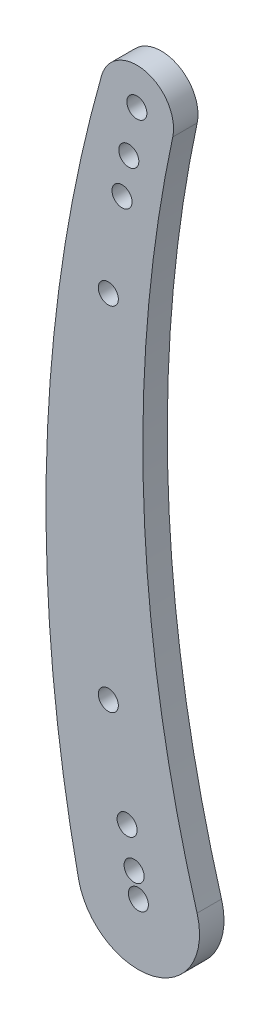
SolidWorks part; units mm, degrees
material "Acrílico (Impacto medio-alto)"
ref_plane "Piano frontale" through (0, 0, 0) normal (0, 0, 1) x (1, 0, 0)
ref_plane "Piano superiore" through (0, 0, 0) normal (0, 1, 0) x (1, 0, 0)
ref_plane "Piano destro" through (0, 0, 0) normal (1, 0, 0) x (0, 0, -1)
sketch "Schizzo1" plane through (0, 0, 0) normal (0, 0, 1) x (1, 0, 0)
  circle A0 centre (0, 0) radius 2.05
  circle A1 centre (-0.3094, 139.9997) radius 2.05
  arc A2 (7.024, 138.4277) -> (-7.5254, 142.0442) centre (-0.3094, 139.9997) ccw
  arc A3 (-12.2223, -2.6202) -> (11.9963, 3.5125) centre (0, 0) ccw
  arc A4 (-7.5254, 142.0442) -> (-12.2223, -2.6202) centre (281.1129, 60.2643) ccw
  arc A5 (7.024, 138.4277) -> (11.9963, 3.5125) centre (275.9157, 80.7886) ccw
  dimension "D1" = 4.1
  dimension "D4" = 15
  dimension "D5" = 25
  dimension "D6" = 600
  dimension "D7" = 550
  dimension "D3" = 140
extrude "Estrusione-Estrusione1" add sketch "Schizzo1" along normal blind 5
sketch "Schizzo2" plane through (0, 0, 5) normal (0, 0, 1) x (1, 0, 0)
  circle A0 centre (-6.1421, 104.1667) radius 2.05
  circle A1 centre (-6.1421, 32.2137) radius 2.05
  dimension "D1" = 4.1
extrude "Taglio-Estrusione1" cut sketch "Schizzo2" against normal up to next
sketch "Sketch1" plane through (0, 0, 5) normal (0, 0, 1) x (1, 0, 0)
  line L0 (-0.3094, 139.9997) -> (-1.9591, 130.644) construction
  line L1 (-1.9591, 130.644) -> (5.4726, 130.644) construction
  circle A0 centre (-0.3094, 139.9997) radius 2.05 construction
  circle A1 centre (-0.3094, 139.9997) radius 2.05
  arc A2 (7.024, 138.4277) -> (11.9963, 3.5125) centre (275.9157, 80.7886) ccw construction
  circle A3 centre (-1.9591, 130.644) radius 2.05
  circle A4 centre (-3.3483, 122.7655) radius 2.05
  dimension "D3" = 4.1
  dimension "D4" = 8
  dimension "D1" = 80
  dimension "D2" = 9.5
extrude "Cut-Extrude1" cut sketch "Sketch1" against normal up to next (5 mm away)
sketch "Sketch2" plane through (0, 0, 5) normal (0, 0, 1) x (1, 0, 0)
  line L0 (-2.6569, 13.9349) -> (-2.3001, 12.0636) construction
  line L1 (-2.3001, 12.0636) -> (-1.9433, 10.1923) construction
  line L2 (-1.9433, 10.1923) -> (-1.5865, 8.321) construction
  line L3 (-1.5865, 8.321) -> (-1.2298, 6.4497) construction
  line L4 (-1.2298, 6.4497) -> (-0.873, 4.5784) construction
  line L5 (-0.873, 4.5784) -> (0, 0) construction
  circle A0 centre (-0.873, 4.5784) radius 2.05
  circle A1 centre (-2.3001, 12.0636) radius 2.05
  point P13 (-6.1421, 32.2137)
  dimension "D1" = 4.1
  dimension "D2" = 4.1
  dimension "D3" = 1.905
  dimension "D4" = 4.6609
extrude "Cut-Extrude2" cut sketch "Sketch2" against normal up to next
